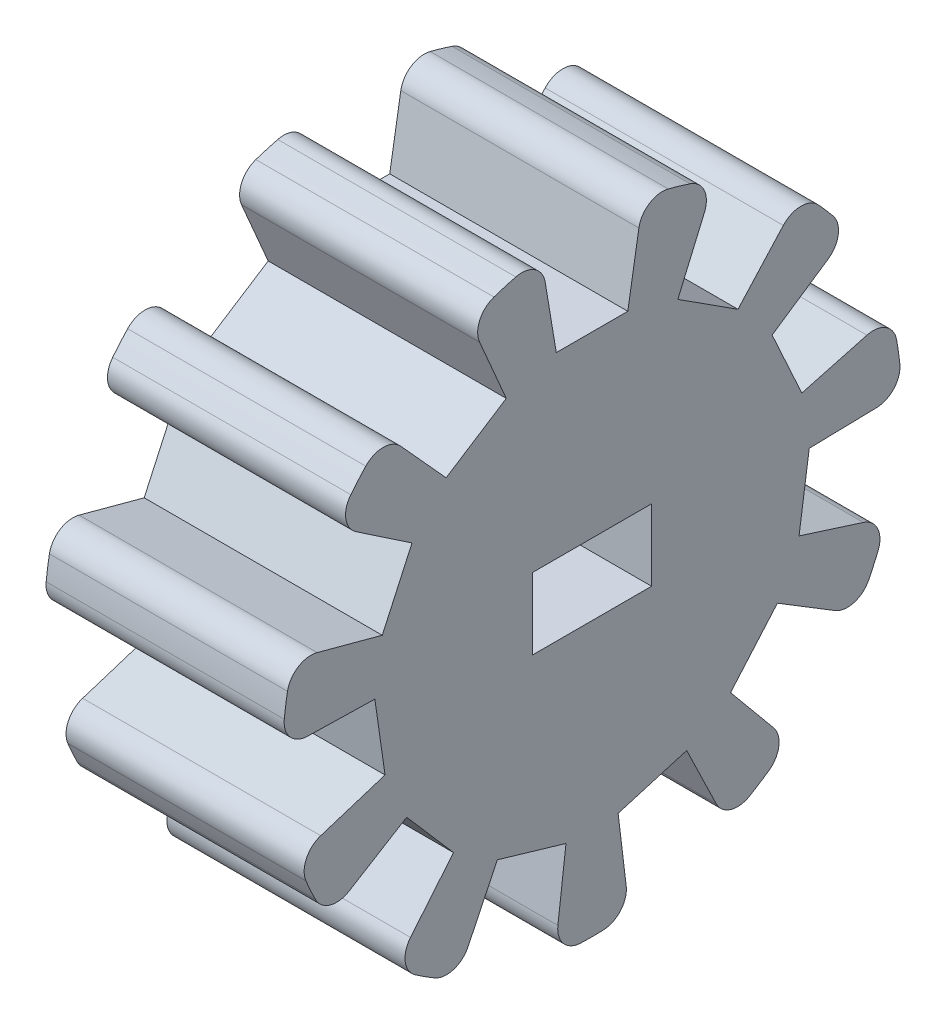
SolidWorks part; units mm, degrees
ref_plane "Front Plane" through (0, 0, 0) normal (0, 0, 1) x (1, 0, 0)
ref_plane "Top Plane" through (0, 0, 0) normal (0, 1, 0) x (1, 0, 0)
ref_plane "Right Plane" through (0, 0, 0) normal (1, 0, 0) x (0, 0, -1)
sketch "Sketch1" plane through (0, 0, 0) normal (0, 0, 1) x (1, 0, 0)
  line L0 (-10, 0) -> (-34.486, 0) construction
  line L1 (0, 0) -> (-10, 0)
  line L2 (-10, 0) -> (-10, 13)
  line L3 (0, 13) -> (0, 0)
  line L7 (-10, 13) -> (0, 13)
  dimension "D2" = 13
revolve "Revolve1" add sketch "Sketch1" angle 360 about L0
sketch "Sketch4" plane through (-10, 0, 0) normal (-1, 0, 0) x (0, 0, 1)
  line L1 (2.5, -1.5) -> (-2.5, -1.5)
  line L6 (2.5, -1.5) -> (2.5, 1.5)
  line L7 (2.5, 1.5) -> (-2.5, 1.5)
  line L8 (-2.5, -1.5) -> (-2.5, 1.5)
  line L9 (2.5, -1.5) -> (-2.5, 1.5) construction
  line L10 (2.5, 1.5) -> (-2.5, -1.5) construction
  point P0 (0, 0)
  point P3 (0, 0)
  point P8 (0, 0)
  dimension "D1" = 3
  dimension "D2" = 5
sketch "Sketch5" plane through (0, 0, 0) normal (1, 0, 0) x (0, 0, -1)
  line L0 (-2.502, 15) -> (2.502, 15)
  line L1 (-1.5018, 9) -> (1.5018, 9)
  line L2 (-2.502, 15) -> (-1.5018, 9)
  line L3 (2.502, 15) -> (1.5018, 9)
  point P6 (0, 9)
  dimension "D1" = 6
  dimension "D2" = 9
sketch "Sketch6" plane through (0, 0, 0) normal (1, 0, 0) x (0, 0, -1)
  line L0 (-1.5018, 9) -> (1.5018, 9)
  line L1 (1.5018, 9) -> (2.502, 15)
  line L2 (2.502, 15) -> (-2.502, 15)
  line L3 (-2.502, 15) -> (-1.5018, 9)
extrude "Cut-Extrude1" cut sketch "Sketch6" against normal blind 10
sketch "Sketch7" plane through (0, 0, 0) normal (1, 0, 0) x (0, 0, -1)
  line L0 (-2.5, 1.5) -> (2.5, 1.5)
  line L1 (2.5, 1.5) -> (2.5, -1.5)
  line L2 (2.5, -1.5) -> (-2.5, -1.5)
  line L3 (-2.5, -1.5) -> (-2.5, 1.5)
extrude "Cut-Extrude2" cut sketch "Sketch7" against normal blind 10
fillet "Fillet1" radius 1 2 edges at (-5, 12.8228, -2.1391) (-5, 12.8228, 2.1391)
pattern_circular "CirPattern1" count 11 over 360 about axis through (0, 0, 0) along (1, 0, 0) of "Fillet1", "Cut-Extrude1"
